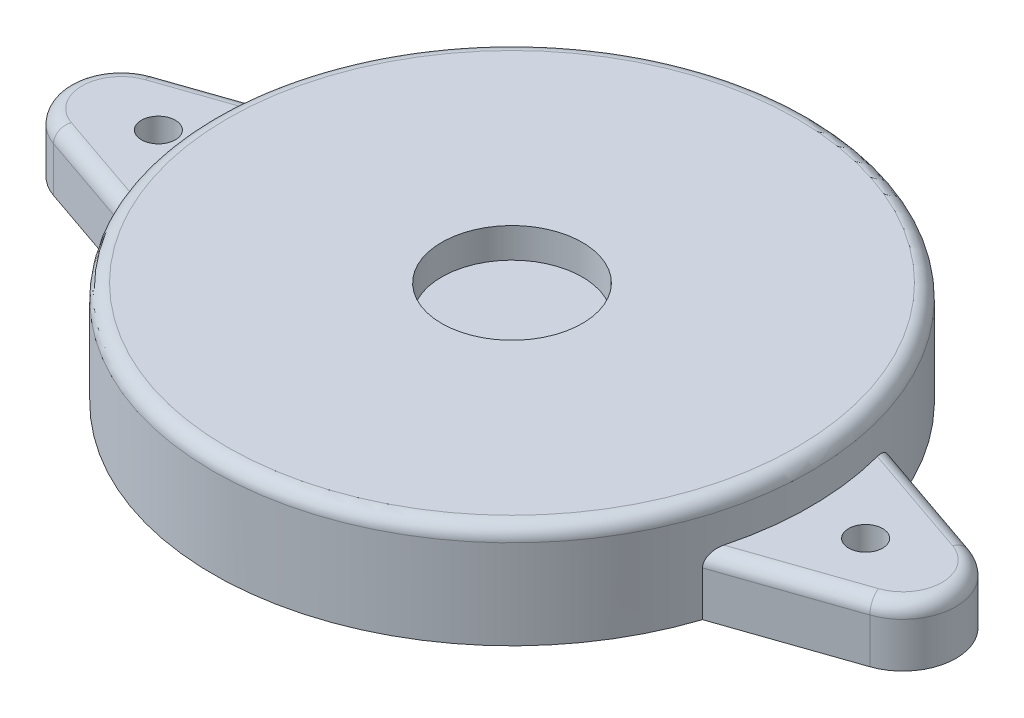
SolidWorks part; units mm, degrees
ref_plane "Front Plane" through (0, 0, 0) normal (0, 0, 1) x (1, 0, 0)
ref_plane "Top Plane" through (0, 0, 0) normal (0, 1, 0) x (1, 0, 0)
ref_plane "Right Plane" through (0, 0, 0) normal (1, 0, 0) x (0, 0, -1)
sketch "Sketch1" plane through (0, 0, 0) normal (0, 1, 0) x (1, 0, 0)
  circle A0 centre (0, 0) radius 14.93
  dimension "D1" = 29.86
extrude "Boss-Extrude1" add sketch "Sketch1" along normal blind 5.16
sketch "Sketch2" plane through (0, 0, 0) normal (0, 1, 0) x (1, 0, 0)
  line L0 (0, 0) -> (0, 19.6223) construction
  line L1 (-14.1842, -4.6597) -> (-20.4067, -2.5149)
  line L2 (14.1842, 4.6597) -> (20.4067, 2.5149)
  line L3 (14.1842, -4.6597) -> (20.4067, -2.5149)
  line L4 (-14.1842, 4.6597) -> (-20.4067, 2.5149)
  circle A0 centre (0, 0) radius 14.93 construction
  arc A1 (14.1842, -4.6597) -> (14.1842, 4.6597) centre (0, 0) ccw
  arc A2 (20.4067, -2.5149) -> (20.4067, 2.5149) centre (19.5399, 0) ccw
  circle A3 centre (17.68, 0) radius 0.85
  circle A4 centre (-17.68, 0) radius 0.85
  arc A5 (-20.4067, -2.5149) -> (-20.4067, 2.5149) centre (-19.5399, 0) cw
  arc A6 (-14.1842, -4.6597) -> (-14.1842, 4.6597) centre (0, 0) cw
  dimension "D1" = 1.7
extrude "Boss-Extrude2" add sketch "Sketch2" along normal blind 2.94
fillet "Fillet2" radius 0.7 1 edges at (0, 5.16, 14.93)
fillet "Fillet4" radius 0.7 6 edges at (-17.2955, 2.94, -3.5873) (-22.2, 2.94, 0) (17.2955, 2.94, -3.5873) (22.2, 2.94, 0) (-17.2955, 2.94, 3.5873) (17.2955, 2.94, 3.5873)
sketch "Sketch3" plane through (0, 5.16, 0) normal (0, 1, 0) x (1, 0, 0)
  circle A0 centre (0, 0) radius 3.515
  dimension "D1" = 7.03
extrude "Cut-Extrude1" cut sketch "Sketch3" against normal blind 1.5
